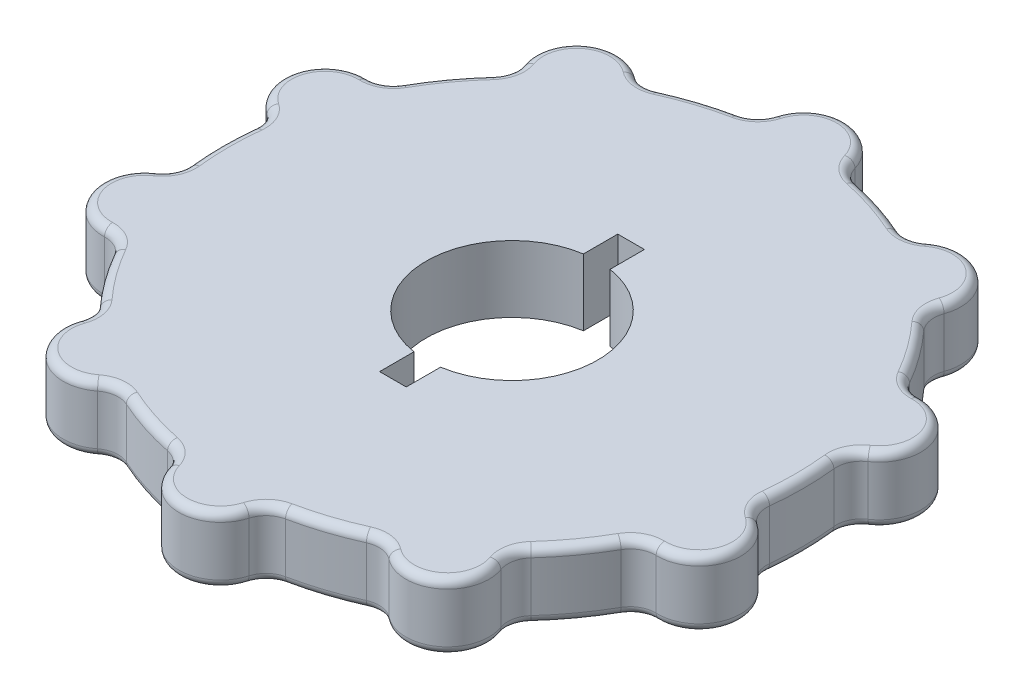
SolidWorks part; units mm, degrees
ref_plane "前视基准面" through (0, 0, 0) normal (0, 0, 1) x (1, 0, 0)
ref_plane "上视基准面" through (0, 0, 0) normal (0, 1, 0) x (1, 0, 0)
ref_plane "右视基准面" through (0, 0, 0) normal (1, 0, 0) x (0, 0, -1)
other "Configuration Table"
sketch "草图1" plane through (0, 0, 0) normal (0, 1, 0) x (1, 0, 0)
  circle A0 centre (0, 0) radius 10.3
  circle A1 centre (0, 0) radius 40
  dimension "D1" = 20.6
  dimension "D2" = 80
extrude "凸台-拉伸1" add sketch "草图1" along normal blind 8
sketch "草图2" plane through (0, 8, 0) normal (0, 1, 0) x (1, 0, 0)
  arc A0 (-7.0805, 34.2763) -> (7.0805, 34.2763) centre (0, 0) ccw
  arc A1 (4.8047, 36.3839) -> (-4.8047, 36.3839) centre (0, 35) ccw
  circle A2 centre (0, 0) radius 40 construction
  circle A3 centre (0, 0) radius 40
  arc A4 (4.8047, 36.3839) -> (7.0805, 34.2763) centre (7.6875, 37.2143) ccw
  arc A5 (-7.0805, 34.2763) -> (-4.8047, 36.3839) centre (-7.6875, 37.2143) ccw
  arc A6 (14.4188, 31.892) -> (17.4989, 32.2593) centre (15.6547, 34.6256) ccw
  arc A7 (25.273, 26.6111) -> (17.4989, 32.2593) centre (20.5725, 28.3156) ccw
  arc A8 (25.273, 26.6111) -> (25.8754, 23.5683) centre (28.0933, 25.5884) ccw
  arc A9 (30.4107, 17.326) -> (33.1185, 15.8128) centre (33.0173, 18.811) ccw
  arc A10 (36.0879, 6.6738) -> (33.1185, 15.8128) centre (33.287, 10.8156) ccw
  arc A11 (36.0879, 6.6738) -> (34.7867, 3.858) centre (37.7684, 4.1886) ccw
  arc A12 (34.7867, -3.858) -> (36.0879, -6.6738) centre (37.7684, -4.1886) ccw
  arc A13 (33.1185, -15.8128) -> (36.0879, -6.6738) centre (33.287, -10.8156) ccw
  arc A14 (33.1185, -15.8128) -> (30.4107, -17.326) centre (33.0173, -18.811) ccw
  arc A15 (25.8754, -23.5683) -> (25.273, -26.6111) centre (28.0933, -25.5884) ccw
  arc A16 (17.4989, -32.2593) -> (25.273, -26.6111) centre (20.5725, -28.3156) ccw
  arc A17 (17.4989, -32.2593) -> (14.4188, -31.892) centre (15.6547, -34.6256) ccw
  arc A18 (7.0805, -34.2763) -> (4.8047, -36.3839) centre (7.6875, -37.2143) ccw
  arc A19 (-4.8047, -36.3839) -> (4.8047, -36.3839) centre (0, -35) ccw
  arc A20 (-4.8047, -36.3839) -> (-7.0805, -34.2763) centre (-7.6875, -37.2143) ccw
  arc A21 (-14.4188, -31.892) -> (-17.4989, -32.2593) centre (-15.6547, -34.6256) ccw
  arc A22 (-25.273, -26.6111) -> (-17.4989, -32.2593) centre (-20.5725, -28.3156) ccw
  arc A23 (-25.273, -26.6111) -> (-25.8754, -23.5683) centre (-28.0933, -25.5884) ccw
  arc A24 (-30.4107, -17.326) -> (-33.1185, -15.8128) centre (-33.0173, -18.811) ccw
  arc A25 (-36.0879, -6.6738) -> (-33.1185, -15.8128) centre (-33.287, -10.8156) ccw
  arc A26 (-36.0879, -6.6738) -> (-34.7867, -3.858) centre (-37.7684, -4.1886) ccw
  arc A27 (-34.7867, 3.858) -> (-36.0879, 6.6738) centre (-37.7684, 4.1886) ccw
  arc A28 (-33.1185, 15.8128) -> (-36.0879, 6.6738) centre (-33.287, 10.8156) ccw
  arc A29 (-33.1185, 15.8128) -> (-30.4107, 17.326) centre (-33.0173, 18.811) ccw
  arc A30 (-25.8754, 23.5683) -> (-25.273, 26.6111) centre (-28.0933, 25.5884) ccw
  arc A31 (-17.4989, 32.2593) -> (-25.273, 26.6111) centre (-20.5725, 28.3156) ccw
  arc A32 (-17.4989, 32.2593) -> (-14.4188, 31.892) centre (-15.6547, 34.6256) ccw
  point P77 (0, 0)
  circle M1 centre (0, 0) radius 40
  dimension "D1" = 70
  dimension "D2" = 3
  dimension "D3" = 3
  dimension "D4" = 10
extrude "切除-拉伸1" cut sketch "草图2" against normal through all contours A28 A3 A25 A26 A0 A27 | A25 A3 A22 A23 A0 A24 | A22 A3 A19 A20 A0 A21 | A19 A3 A16 A17 A0 A18 | A16 A3 A13 A14 A0 A15 | A13 A3 A10 A11 A0 A12 | A10 A3 A7 A8 A0 A9 | A7 A3 A1 A4 A0 A6 | A31 A32 A0 A5 A1 M1 | A31 A3 A28 A29 A0 A30
fillet "圆角1" radius 1 80 edges at (-25.1504, 0, 25.0058) (-28.3156, 0, 20.5725) (-31.5538, 0, 16.1922) (-38.0423, 0, 12.3607) (-35.0451, 0, 5.4471) (-35, 0, 0) (-35.0451, 0, -5.4471) (-38.0423, 0, -12.3607) (-31.5538, 0, -16.1922) (-28.3156, 0, -20.5725) (-25.1504, 0, -25.0058) (-23.5114, 0, -32.3607) (-16.01, 0, -31.6467) (-10.8156, 0, -33.287) (-5.6491, 0, -35.0132) (0, 0, -40) (5.6491, 0, -35.0132) (10.8156, 0, -33.287) (16.01, 0, -31.6467) (23.5114, 0, -32.3607) (25.1504, 0, -25.0058) (28.3156, 0, -20.5725) (31.5538, 0, -16.1922) (38.0423, 0, -12.3607) (35.0451, 0, -5.4471) (35, 0, 0) (35.0451, 0, 5.4471) (38.0423, 0, 12.3607) (31.5538, 0, 16.1922) (28.3156, 0, 20.5725) (25.1504, 0, 25.0058) (23.5114, 0, 32.3607) (16.01, 0, 31.6467) (10.8156, 0, 33.287) (5.6491, 0, 35.0132) (0, 0, 40) (-5.6491, 0, 35.0132) (-10.8156, 0, 33.287) (-16.01, 0, 31.6467) (-35.0451, 8, 5.4471) (-35, 8, 0) (-35.0451, 8, -5.4471) (-38.0423, 8, -12.3607) (-31.5538, 8, -16.1922) (-28.3156, 8, -20.5725) (-25.1504, 8, -25.0058) (-23.5114, 8, -32.3607) (-16.01, 8, -31.6467) (-10.8156, 8, -33.287) (-5.6491, 8, -35.0132) (0, 8, -40) (5.6491, 8, -35.0132) (10.8156, 8, -33.287) (16.01, 8, -31.6467) (23.5114, 8, -32.3607) (25.1504, 8, -25.0058) (28.3156, 8, -20.5725) (31.5538, 8, -16.1922) (38.0423, 8, -12.3607) (35.0451, 8, -5.4471) (35, 8, 0) (35.0451, 8, 5.4471) (38.0423, 8, 12.3607) (31.5538, 8, 16.1922) (28.3156, 8, 20.5725) (25.1504, 8, 25.0058) (23.5114, 8, 32.3607) (16.01, 8, 31.6467) (10.8156, 8, 33.287) (5.6491, 8, 35.0132) (0, 8, 40) (-5.6491, 8, 35.0132) (-10.8156, 8, 33.287) (-16.01, 8, 31.6467) (-23.5114, 8, 32.3607) (-25.1504, 8, 25.0058) (-28.3156, 8, 20.5725) (-31.5538, 8, 16.1922) (-23.5114, 0, 32.3607) (-38.0423, 8, 12.3607)
sketch "草图3" plane through (0, 0, 0) normal (0, -1, 0) x (1, 0, 0)
  line L1 (-1.6, 14.3) -> (1.6, 14.3)
  line L2 (-1.6, 14.3) -> (-1.6, 6.3)
  line L3 (-1.6, 6.3) -> (1.6, 6.3)
  line L4 (1.6, 14.3) -> (1.6, 6.3)
  line L5 (-1.6, 14.3) -> (1.6, 6.3) construction
  line L6 (-1.6, 6.3) -> (1.6, 14.3) construction
  circle A0 centre (0, 0) radius 10.3 construction
  point P0 (0, 10.3)
  dimension "D1" = 3.2
  dimension "D2" = 8
extrude "切除-拉伸2" cut sketch "草图3" against normal through all
pattern_circular "阵列(圆周)1" count 2 over 360 about axis through (0, 0, 0) along (0, 1, 0) of "切除-拉伸2"
